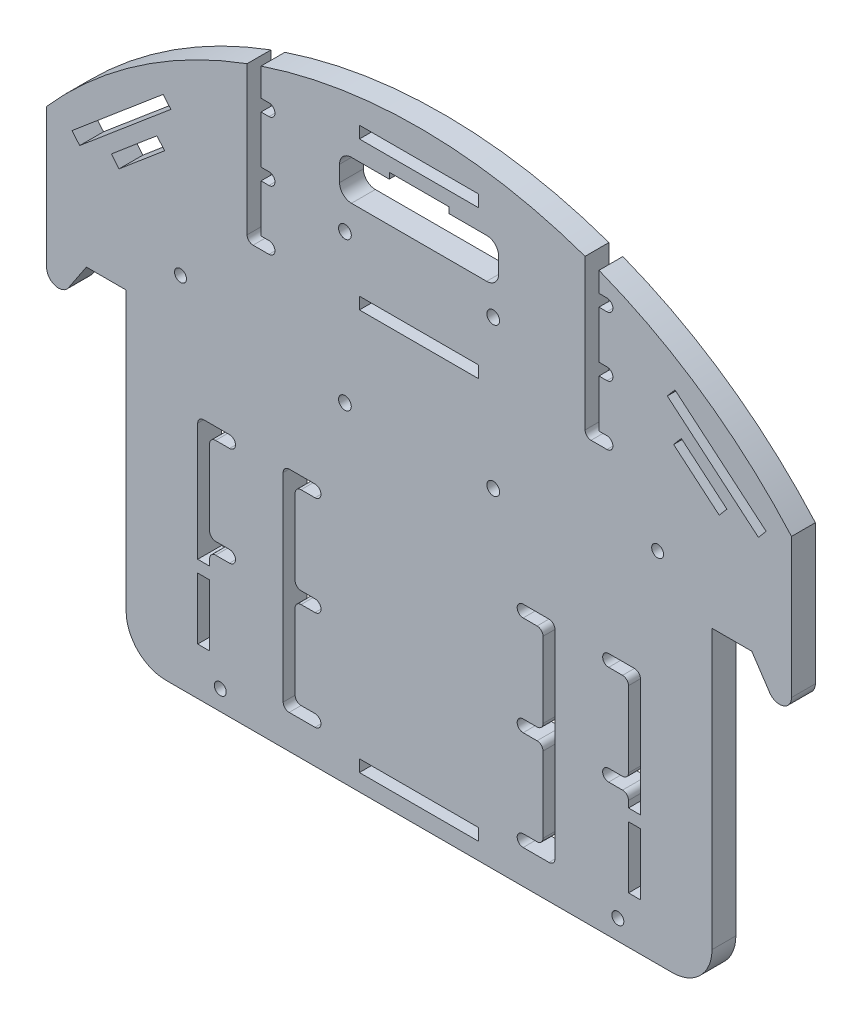
SolidWorks part; units mm, degrees
ref_plane "Front" through (0, 0, 0) normal (0, 0, 1) x (1, 0, 0)
ref_plane "Top" through (0, 0, 0) normal (0, 1, 0) x (1, 0, 0)
ref_plane "Right" through (0, 0, 0) normal (1, 0, 0) x (0, 0, -1)
sketch "Sketch1" plane through (0, 0, 0) normal (0, 0, 1) x (1, 0, 0)
  line L0 (-73.675, -35) -> (73.675, -35)
  line L1 (93.675, 82.7647) -> (93.675, 35)
  line L2 (-93.675, 35) -> (-93.675, 82.7647)
  line L3 (0, 1.001) -> (0, -10.9817) construction
  line L5 (0, 0) -> (-129.3874, 0) construction
  line L6 (-73.675, 35) -> (-93.675, 35)
  line L7 (-73.675, 35) -> (-73.675, -35)
  line L9 (73.675, 35) -> (93.675, 35)
  line L10 (73.675, 35) -> (73.675, -35)
  arc A1 (93.675, 82.7647) -> (-93.675, 82.7647) centre (0, 0) ccw
  point P9 (-64.6937, 0)
  point P10 (55, 0)
  point P11 (-55, 0)
  dimension "D1" = 250
  dimension "D5" = 20
  dimension "D6" = 20
  dimension "D7" = 70
  dimension "D9" = 35
extrude "Boss-Extrude1" add sketch "Sketch1" along normal blind 6
sketch "Sketch2" plane through (0, 0, 6) normal (0, 0, 1) x (1, 0, 0)
  line L0 (0, -35) -> (0, 125) construction
  line L1 (-73.675, -35) -> (73.675, -35) construction
  line L2 (-37.75, 78.5) -> (-39.75, 78.5)
  line L3 (-43.25, 78.5) -> (-43.25, 119.0294)
  line L4 (-39.75, 81.5) -> (-39.75, 93.5)
  line L5 (-39.75, 78.5) -> (-43.25, 78.5)
  line L6 (-43.25, 119.0294) -> (-39.75, 119.0294)
  line L7 (-37.75, 81.5) -> (-39.25, 81.5)
  line L8 (-39.25, 93.5) -> (-37.75, 93.5)
  line L9 (-37.75, 96.5) -> (-39.25, 96.5)
  line L10 (-39.25, 108.5) -> (-37.75, 108.5)
  line L11 (-37.75, 111.5) -> (-39.25, 111.5)
  line L12 (-39.75, 111.5) -> (-39.75, 119.0294)
  line L13 (-39.75, 96.5) -> (-39.75, 108.5)
  line L14 (41.75, 119.0294) -> (41.75, 119.6207)
  line L15 (41.75, 119.6207) -> (45.25, 119.6207)
  line L16 (45.25, 119.6207) -> (45.25, 119.0294)
  line L17 (47.25, 78.5) -> (41.75, 78.5)
  line L18 (47.25, 81.5) -> (45.25, 81.5)
  line L19 (41.75, 78.5) -> (41.75, 119.0294)
  line L20 (45.25, 119.0294) -> (45.25, 111.5)
  line L21 (47.25, 111.5) -> (45.25, 111.5)
  line L22 (47.25, 108.5) -> (45.25, 108.5)
  line L23 (47.25, 96.5) -> (45.25, 96.5)
  line L24 (47.25, 93.5) -> (45.25, 93.5)
  line L25 (45.25, 93.5) -> (45.25, 81.5)
  line L26 (-39.25, 111.5) -> (-39.75, 111.5)
  line L27 (-39.25, 108.5) -> (-39.75, 108.5)
  line L28 (-39.25, 96.5) -> (-39.75, 96.5)
  line L29 (-39.25, 93.5) -> (-39.75, 93.5)
  line L30 (-39.25, 81.5) -> (-39.75, 81.5)
  line L31 (45.25, 108.5) -> (45.25, 96.5)
  arc A0 (93.675, 82.7647) -> (-93.675, 82.7647) centre (0, 0) ccw construction
  arc A1 (-37.75, 78.5) -> (-37.75, 81.5) centre (-37.75, 80) ccw
  arc A2 (47.25, 78.5) -> (47.25, 81.5) centre (47.25, 80) ccw
  arc A3 (-37.75, 93.5) -> (-37.75, 96.5) centre (-37.75, 95) ccw
  arc A4 (-37.75, 108.5) -> (-37.75, 111.5) centre (-37.75, 110) ccw
  arc A5 (47.25, 93.5) -> (47.25, 96.5) centre (47.25, 95) ccw
  arc A6 (47.25, 108.5) -> (47.25, 111.5) centre (47.25, 110) ccw
  dimension "D1" = 3
  dimension "D2" = 43.25
  dimension "D3" = 45
  dimension "D4" = 46.5
  dimension "D6" = 2
  dimension "D7" = 3.5
  dimension "D8" = 5.5
  dimension "D10" = 2
  dimension "D11" = 41.75
  dimension "D5" = 3
extrude "Cut-Extrude1" cut sketch "Sketch2" against normal blind 6
sketch "Sketch3" plane through (0, 0, 6) normal (0, 0, 1) x (1, 0, 0)
  line L2 (93.675, 52.7647) -> (73.675, 52.7647)
  line L3 (73.675, 52.7647) -> (73.675, -27.2353)
  line L6 (93.675, -16.1176) -> (93.675, 52.7647)
  line L7 (0, 0) -> (0, 58.8824) construction
  line L8 (-93.675, -16.1176) -> (-93.675, 52.7647)
  line L10 (-73.675, 52.7647) -> (-73.675, -27.2353)
  line L11 (-93.675, 52.7647) -> (-73.675, 52.7647)
  line L12 (-73.675, -27.2353) -> (73.675, -27.2353)
  line L13 (73.675, -35) -> (-73.675, -35)
  line L15 (-93.675, -16.1176) -> (-93.675, -35)
  line L16 (-93.675, -35) -> (-73.675, -35)
  line L17 (93.675, -16.1176) -> (93.675, -35)
  line L18 (93.675, -35) -> (73.675, -35)
  dimension "D1" = 30
  dimension "D2" = 80
extrude "Cut-Extrude2" cut sketch "Sketch3" against normal blind 6
sketch "Sketch4" plane through (0, 0, 6) normal (0, 0, 1) x (1, 0, 0)
  line L1 (0, 0) -> (0, -8.7341) construction
  line L2 (93.675, 52.7647) -> (73.675, 52.7647) construction
  circle A0 centre (50, -22.2353) radius 1.5
  circle A1 centre (-50, -22.2353) radius 1.5
  circle A2 centre (60, 62.7647) radius 1.5
  circle A3 centre (-60, 62.7647) radius 1.5
  dimension "D1" = 10
  dimension "D2" = 50
  dimension "D3" = 3
  dimension "D4" = 85
  dimension "D5" = 60
extrude "Cut-Extrude3" cut sketch "Sketch4" against normal blind 6
sketch "Sketch5" plane through (0, 0, 6) normal (0, 0, 1) x (1, 0, 0)
  line L1 (-17, 110) -> (17, 110)
  line L2 (-20, 107) -> (-20, 103)
  line L3 (-17, 100) -> (17, 100)
  line L4 (20, 107) -> (20, 103)
  line L5 (-20, 110) -> (20, 100) construction
  line L6 (-20, 100) -> (20, 110) construction
  arc A0 (17, 110) -> (20, 107) centre (17, 107) cw
  arc A1 (17, 100) -> (20, 103) centre (17, 103) ccw
  arc A2 (-20, 103) -> (-17, 100) centre (-17, 103) ccw
  arc A3 (-17, 110) -> (-20, 107) centre (-17, 107) ccw
  point P0 (0, 105)
  dimension "D4" = 3
  dimension "D1" = 40
  dimension "D2" = 105
  dimension "D3" = 10
extrude "Cut-Extrude4" cut sketch "Sketch5" against normal blind 6
sketch "Sketch6" plane through (0, 0, 0) normal (0, 0, -1) x (-1, 0, 0)
  line L1 (-15, 80.7647) -> (15, 80.7647)
  line L2 (-15, 80.7647) -> (-15, 77.7647)
  line L3 (-15, 77.7647) -> (15, 77.7647)
  line L4 (15, 80.7647) -> (15, 77.7647)
extrude "Cut-Extrude5" cut sketch "Sketch6" against normal blind 6
sketch "Sketch9" plane through (0, 0, 6) normal (0, 0, 1) x (1, 0, 0)
  line L0 (17, 110) -> (-17, 110) construction
  line L1 (-15, 118) -> (15, 118)
  line L2 (-15, 118) -> (-15, 115)
  line L3 (-15, 115) -> (15, 115)
  line L4 (15, 118) -> (15, 115)
  line L5 (-15, 118) -> (15, 115) construction
  line L6 (-15, 115) -> (15, 118) construction
  line L7 (-20, 107) -> (-20, 103) construction
  line L8 (0, 115) -> (0, 110) construction
  line L9 (64.3643, 100.03) -> (87.2946, 80.6856)
  line L10 (64.3643, 100.03) -> (62.4299, 97.7369)
  line L11 (62.4299, 97.7369) -> (85.3602, 78.3926)
  line L12 (87.2946, 80.6856) -> (85.3602, 78.3926)
  line L13 (64.3643, 100.03) -> (85.3602, 78.3926) construction
  line L14 (62.4299, 97.7369) -> (87.2946, 80.6856) construction
  line L15 (0, 0) -> (0, 41.6685) construction
  line L16 (-62.4299, 97.7369) -> (-87.2946, 80.6856) construction
  line L17 (-64.3643, 100.03) -> (-85.3602, 78.3926) construction
  line L18 (-87.2946, 80.6856) -> (-85.3602, 78.3926)
  line L19 (-62.4299, 97.7369) -> (-85.3602, 78.3926)
  line L20 (-64.3643, 100.03) -> (-62.4299, 97.7369)
  line L21 (-64.3643, 100.03) -> (-87.2946, 80.6856)
  line L22 (65.9603, 90.2626) -> (77.4228, 80.5874)
  line L23 (-7.5, 111.5) -> (7.5, 111.5)
  line L24 (-7.5, 111.5) -> (-7.5, 108.5)
  line L25 (-7.5, 108.5) -> (7.5, 108.5)
  line L26 (7.5, 111.5) -> (7.5, 108.5)
  line L27 (-7.5, 111.5) -> (7.5, 108.5) construction
  line L28 (-7.5, 108.5) -> (7.5, 111.5) construction
  line L29 (65.9603, 90.2626) -> (64.0252, 87.9701)
  line L30 (64.0252, 87.9701) -> (75.4878, 78.2949)
  line L31 (77.4228, 80.5874) -> (75.4878, 78.2949)
  line L32 (65.9603, 90.2626) -> (75.4878, 78.2949) construction
  line L33 (64.0252, 87.9701) -> (77.4228, 80.5874) construction
  line L34 (-77.394, 80.5528) -> (-65.9324, 90.2291)
  line L35 (-77.394, 80.5528) -> (-75.4588, 78.2604)
  line L36 (-75.4588, 78.2604) -> (-63.9971, 87.9367)
  line L37 (-65.9324, 90.2291) -> (-63.9971, 87.9367)
  line L38 (-77.394, 80.5528) -> (-63.9971, 87.9367) construction
  line L39 (-75.4588, 78.2604) -> (-65.9324, 90.2291) construction
  point P0 (0, 116.5)
  point P9 (-20, 105)
  point P15 (74.8623, 89.2113)
  point P20 (0.0972, 0.436)
  point P23 (-74.8623, 89.2113)
  point P38 (0.187, 0.4209)
  point P43 (-0.1315, 0.4571)
  dimension "D1" = 3
  dimension "D2" = 5
  dimension "D3" = 30
  dimension "D4" = 5
  dimension "D5" = 2
  dimension "D6" = 5
  dimension "D7" = 3
  dimension "D8" = 15
  dimension "D9" = 2
  dimension "D10" = 2
extrude "Cut-Extrude8" cut sketch "Sketch9" against normal blind 10
sketch "Sketch11" plane through (0, 0, 6) normal (0, 0, 1) x (1, 0, 0)
  line L0 (-47.675, -18.7353) -> (-54.175, -18.7353)
  line L1 (-55.675, -17.2353) -> (-55.675, 32.7647)
  line L2 (-54.175, 34.2647) -> (-47.675, 34.2647)
  line L3 (-47.675, -15.7353) -> (-51.175, -15.7353)
  line L4 (-52.675, -14.2353) -> (-52.675, 4.7647)
  line L5 (-51.175, 31.2647) -> (-47.675, 31.2647)
  line L6 (-47.675, 6.2647) -> (-51.175, 6.2647)
  line L7 (-47.675, 9.2647) -> (-51.175, 9.2647)
  line L8 (-52.675, 10.7647) -> (-52.675, 29.7647)
  line L9 (-31.175, -14.2353) -> (-31.175, 4.7647)
  line L10 (-26.175, 6.2647) -> (-29.675, 6.2647)
  line L11 (-26.175, -15.7353) -> (-29.675, -15.7353)
  line L12 (-26.175, 9.2647) -> (-29.675, 9.2647)
  line L13 (-26.175, -18.7353) -> (-32.675, -18.7353)
  line L14 (-32.675, 34.2647) -> (-26.175, 34.2647)
  line L15 (-31.175, 10.7647) -> (-31.175, 29.7647)
  line L16 (-34.175, -17.2353) -> (-34.175, 32.7647)
  line L17 (-29.675, 31.2647) -> (-26.175, 31.2647)
  line L18 (0, 0) -> (0, 36.0933) construction
  line L19 (29.675, 31.2647) -> (26.175, 31.2647)
  line L20 (34.175, -17.2353) -> (34.175, 32.7647)
  line L21 (31.175, 10.7647) -> (31.175, 29.7647)
  line L22 (32.675, 34.2647) -> (26.175, 34.2647)
  line L23 (26.175, -18.7353) -> (32.675, -18.7353)
  line L24 (26.175, 9.2647) -> (29.675, 9.2647)
  line L25 (26.175, -15.7353) -> (29.675, -15.7353)
  line L26 (26.175, 6.2647) -> (29.675, 6.2647)
  line L27 (31.175, -14.2353) -> (31.175, 4.7647)
  line L28 (52.675, 10.7647) -> (52.675, 29.7647)
  line L29 (47.675, 9.2647) -> (51.175, 9.2647)
  line L30 (47.675, 6.2647) -> (51.175, 6.2647)
  line L31 (51.175, 31.2647) -> (47.675, 31.2647)
  line L32 (52.675, -14.2353) -> (52.675, 4.7647)
  line L33 (47.675, -15.7353) -> (51.175, -15.7353)
  line L34 (54.175, 34.2647) -> (47.675, 34.2647)
  line L35 (55.675, -17.2353) -> (55.675, 32.7647)
  line L36 (47.675, -18.7353) -> (54.175, -18.7353)
  line L37 (73.675, -27.2353) -> (73.675, 52.7647) construction
  line L40 (55.675, -14.2353) -> (55.675, -17.2353)
  arc A0 (-34.175, 32.7647) -> (-32.675, 34.2647) centre (-32.675, 32.7647) cw
  arc A1 (-32.675, -18.7353) -> (-34.175, -17.2353) centre (-32.675, -17.2353) cw
  arc A2 (-31.175, 29.7647) -> (-29.675, 31.2647) centre (-29.675, 29.7647) cw
  arc A3 (-55.675, 32.7647) -> (-54.175, 34.2647) centre (-54.175, 32.7647) cw
  arc A4 (-52.675, 29.7647) -> (-51.175, 31.2647) centre (-51.175, 29.7647) cw
  arc A5 (-51.175, 9.2647) -> (-52.675, 10.7647) centre (-51.175, 10.7647) cw
  arc A6 (-51.175, 6.2647) -> (-52.675, 4.7647) centre (-51.175, 4.7647) ccw
  arc A7 (-54.175, -18.7353) -> (-55.675, -17.2353) centre (-54.175, -17.2353) cw
  arc A8 (-51.175, -15.7353) -> (-52.675, -14.2353) centre (-51.175, -14.2353) cw
  arc A9 (-47.675, 31.2647) -> (-47.675, 34.2647) centre (-47.675, 32.7647) ccw
  arc A10 (-47.675, 6.2647) -> (-47.675, 9.2647) centre (-47.675, 7.7647) ccw
  arc A11 (-47.675, -18.7353) -> (-47.675, -15.7353) centre (-47.675, -17.2353) ccw
  arc A12 (-29.675, -15.7353) -> (-31.175, -14.2353) centre (-29.675, -14.2353) cw
  arc A13 (-29.675, 9.2647) -> (-31.175, 10.7647) centre (-29.675, 10.7647) cw
  arc A14 (-29.675, 6.2647) -> (-31.175, 4.7647) centre (-29.675, 4.7647) ccw
  arc A15 (-26.175, 31.2647) -> (-26.175, 34.2647) centre (-26.175, 32.7647) ccw
  arc A16 (-26.175, 6.2647) -> (-26.175, 9.2647) centre (-26.175, 7.7647) ccw
  arc A17 (-26.175, -18.7353) -> (-26.175, -15.7353) centre (-26.175, -17.2353) ccw
  arc A18 (26.175, -18.7353) -> (26.175, -15.7353) centre (26.175, -17.2353) cw
  arc A19 (26.175, 6.2647) -> (26.175, 9.2647) centre (26.175, 7.7647) cw
  arc A20 (26.175, 31.2647) -> (26.175, 34.2647) centre (26.175, 32.7647) cw
  arc A21 (29.675, 6.2647) -> (31.175, 4.7647) centre (29.675, 4.7647) cw
  arc A22 (29.675, 9.2647) -> (31.175, 10.7647) centre (29.675, 10.7647) ccw
  arc A23 (29.675, -15.7353) -> (31.175, -14.2353) centre (29.675, -14.2353) ccw
  arc A24 (47.675, -18.7353) -> (47.675, -15.7353) centre (47.675, -17.2353) cw
  arc A25 (47.675, 6.2647) -> (47.675, 9.2647) centre (47.675, 7.7647) cw
  arc A26 (47.675, 31.2647) -> (47.675, 34.2647) centre (47.675, 32.7647) cw
  arc A27 (51.175, -15.7353) -> (52.675, -14.2353) centre (51.175, -14.2353) ccw
  arc A28 (54.175, -18.7353) -> (55.675, -17.2353) centre (54.175, -17.2353) ccw
  arc A29 (51.175, 6.2647) -> (52.675, 4.7647) centre (51.175, 4.7647) cw
  arc A30 (51.175, 9.2647) -> (52.675, 10.7647) centre (51.175, 10.7647) ccw
  arc A31 (52.675, 29.7647) -> (51.175, 31.2647) centre (51.175, 29.7647) ccw
  arc A32 (55.675, 32.7647) -> (54.175, 34.2647) centre (54.175, 32.7647) ccw
  arc A33 (31.175, 29.7647) -> (29.675, 31.2647) centre (29.675, 29.7647) ccw
  arc A34 (32.675, -18.7353) -> (34.175, -17.2353) centre (32.675, -17.2353) ccw
  arc A35 (34.175, 32.7647) -> (32.675, 34.2647) centre (32.675, 32.7647) ccw
  point P24 (-52.675, 9.2647)
  point P29 (-55.675, -18.7353)
  point P113 (55.675, -18.7353)
  point P114 (52.675, 9.2647)
  point P117 (46.175, 32.7647)
  point P118 (55.675, 0.6169)
  dimension "D3" = 1.5
  dimension "D5" = 1.5
  dimension "D1" = 3
  dimension "D2" = 8
  dimension "D4" = 3
  dimension "D6" = 18
  dimension "D7" = 12
extrude "Cut-Extrude13" cut sketch "Sketch11" against normal blind 10 contours L13 A17 L11 A12 L9 A14 L10 A16 L12 A13 L15 A2 L17 A15 L14 A0 L16 A1 | L20 A35 L22 A20 L19 A33 L21 A22 L24 A19 L26 A21 L27 A23 L25 A18 L23 A34 | L35 A32 L34 A26 L31 A31 L28 A30 L29 A25 L30 A29 L32 A27 L33 A24 L36 A28 | L1 A3 L2 A9 L5 A4 L8 A5 L7 A10 L6 A6 L4 A8 L3 A11 L0 A7
sketch "Sketch12" plane through (0, 0, 6) normal (0, 0, 1) x (1, 0, 0)
  line L0 (-93.675, 52.7647) -> (-93.675, 37.7647)
  line L1 (-93.675, 37.7647) -> (-83.675, 52.7647)
  line L2 (-73.675, 52.7647) -> (-93.675, 52.7647) construction
  line L3 (-83.675, 52.7647) -> (-93.675, 52.7647)
  line L4 (83.675, 52.7647) -> (93.675, 52.7647)
  line L5 (93.675, 52.7647) -> (73.675, 52.7647) construction
  line L6 (93.675, 52.7647) -> (93.675, 37.7647)
  line L7 (93.675, 37.7647) -> (83.675, 52.7647)
  dimension "D1" = 15
  dimension "D2" = 15
sketch "Sketch15" plane through (0, 0, 6) normal (0, 0, 1) x (1, 0, 0)
  line L3 (-55.675, -18.7353) -> (-46.175, -18.7353)
  line L8 (46.175, -18.7353) -> (55.675, -18.7353)
  line L10 (55.675, -18.7353) -> (55.675, -12.6681)
  line L11 (55.675, -17.2353) -> (55.675, 32.7647) construction
  line L12 (55.675, -12.6681) -> (46.175, -12.6681)
  line L13 (46.175, -12.6681) -> (46.175, -18.7353)
  line L14 (-55.675, -18.7353) -> (-55.675, -13.8526)
  line L15 (-55.675, -17.2353) -> (-55.675, 32.7647) construction
  line L16 (-55.675, -13.8526) -> (-46.175, -13.8526)
  line L17 (-46.175, -13.8526) -> (-46.175, -18.7353)
extrude "Boss-Extrude5" add sketch "Sketch15" against normal blind 6
extrude "Boss-Extrude2" add sketch "Sketch12" against normal blind 6
fillet "Fillet1" radius 10 2 edges at (73.675, -27.2353, 3) (-73.675, -27.2353, 3)
sketch "Sketch13" plane through (0, 0, 0) normal (0, 0, -1) x (-1, 0, 0)
  line L0 (18.65, 93) -> (-18.65, 93) construction
  line L1 (-18.65, 93) -> (18.65, 55.7) construction
  line L2 (-18.65, 55.7) -> (18.65, 93) construction
  line L3 (17, 100) -> (-17, 100) construction
  circle A0 centre (-18.65, 93) radius 1.6
  circle A1 centre (18.65, 55.7) radius 1.6
  circle A2 centre (-18.65, 55.7) radius 1.6
  circle A3 centre (18.65, 93) radius 1.6
  point P10 (0, 100)
  point P11 (0, 74.35)
  dimension "D5" = 7
  dimension "D6" = 3.2
  dimension "D7" = 3.2
  dimension "D8" = 3.2
  dimension "D9" = 3.2
  dimension "D1" = 37.3
  dimension "D2" = 37.3
  dimension "D3" = 37.3
  dimension "D4" = 37.3
extrude "Cut-Extrude11" cut sketch "Sketch13" against normal blind 6
sketch "Sketch14" plane through (0, 0, 6) normal (0, 0, 1) x (1, 0, 0)
  line L1 (-15, -20) -> (15, -20)
  line L2 (-15, -20) -> (-15, -23)
  line L3 (-15, -23) -> (15, -23)
  line L4 (15, -20) -> (15, -23)
  line L5 (-15, 118) -> (-15, 115) construction
  line L6 (-15, 115) -> (15, 115) construction
  dimension "D1" = 3
  dimension "D2" = 30
  dimension "D3" = 30
  dimension "D4" = 135
extrude "Cut-Extrude12" cut sketch "Sketch14" against normal blind 6
fillet "Fillet2" radius 3 2 edges at (-93.675, 37.7647, 3) (93.675, 37.7647, 3)
fillet "Fillet3" radius 1.5 2 edges at (41.75, 78.5, 3) (-43.25, 78.5, 3)
sketch "Sketch16" plane through (0, 0, 6) normal (0, 0, 1) x (1, 0, 0)
  line L0 (-55.675, -13.8526) -> (-55.675, -15.3526)
  line L1 (-55.675, -15.3526) -> (-52.675, -15.3526)
  line L2 (-52.675, -15.3526) -> (-52.675, -13.8526)
  line L3 (-52.675, -13.8526) -> (-55.675, -13.8526)
  line L4 (52.675, -15.3841) -> (55.675, -15.3841)
  line L6 (55.675, -15.3841) -> (55.675, -12.6681)
  line L7 (55.675, -12.6681) -> (52.675, -12.6681)
  line L8 (52.675, -12.6681) -> (52.675, -15.3841)
  dimension "D1" = 3
  dimension "D2" = 1.5
  dimension "D3" = 3
extrude "Cut-Extrude14" cut sketch "Sketch16" against normal blind 6
sketch "Sketch17" plane through (0, 0, 6) normal (0, 0, 1) x (1, 0, 0)
  line L0 (55.675, -15.3841) -> (55.675, 32.7647) construction
  line L1 (55.675, -15.3841) -> (55.675, 0.1159)
  line L2 (55.675, 0.1159) -> (52.675, 0.1159)
  line L3 (52.675, -15.3841) -> (52.675, 4.7647) construction
  line L4 (52.675, 0.1159) -> (52.675, 3.1159)
  line L5 (52.675, 3.1159) -> (55.675, 3.1159)
  line L6 (55.675, 3.1159) -> (55.675, 0.1159)
  line L7 (0, 0) -> (0, -20) construction
  line L8 (15, -20) -> (-15, -20) construction
  line L9 (-55.675, 3.1159) -> (-55.675, 0.1159)
  line L10 (-52.675, 3.1159) -> (-55.675, 3.1159)
  line L11 (-52.675, 0.1159) -> (-52.675, 3.1159)
  line L12 (-55.675, 0.1159) -> (-52.675, 0.1159)
  dimension "D1" = 15.5
  dimension "D2" = 3
extrude "Boss-Extrude6" add sketch "Sketch17" against normal blind 6 contours L9 L12 L11 L10 | L6 L5 L4 L2
